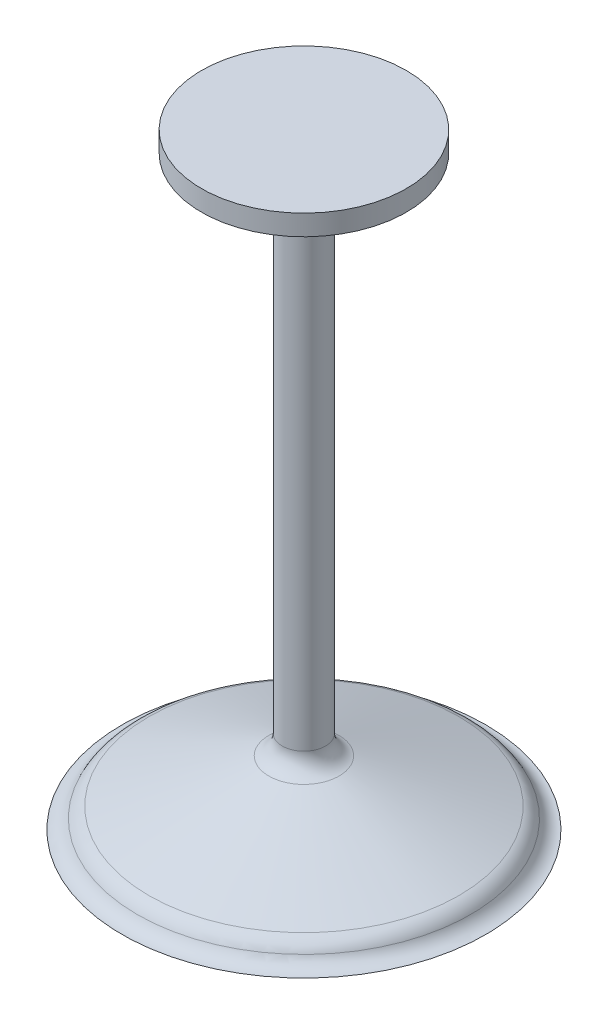
SolidWorks part; units mm, degrees
material "Plain Carbon Steel"
ref_plane "Front Plane" through (0, 0, 0) normal (0, 0, 1) x (1, 0, 0)
ref_plane "Top Plane" through (0, 0, 0) normal (0, 1, 0) x (1, 0, 0)
ref_plane "Right Plane" through (0, 0, 0) normal (1, 0, 0) x (0, 0, -1)
sketch "Sketch1" plane through (0, 0, 0) normal (0, 0, 1) x (1, 0, 0)
  line L0 (-44.8846, 0) -> (44.8846, 0) construction
  line L1 (0, -88.8) -> (0, 88.8) construction
  line L2 (23.5181, 0) -> (26.625, 0)
  line L3 (26.625, 0) -> (26.625, 2.45) construction
  line L4 (26.625, 2.45) -> (24.175, 2.45) construction
  line L5 (22.7023, 2.986) -> (5.1489, 9.3749)
  line L6 (3.175, 12.194) -> (3.175, 85.8)
  line L7 (3.175, 85.8) -> (15, 85.8)
  line L8 (15, 85.8) -> (15, 88.8)
  line L9 (15, 88.8) -> (0, 88.8)
  line L10 (0, 88.8) -> (0, 5)
  line L11 (0, 5) -> (19, 0) construction
  arc A0 (0, 5) -> (15.6481, 1.6135) centre (-0.9184, -37.09) cw
  arc A1 (24.4003, 1.4237) -> (26.625, 0) centre (26.625, 2.45) ccw
  arc A2 (24.4003, 1.4237) -> (22.7023, 2.986) centre (21.6763, 0.1669) ccw
  arc A3 (3.175, 12.194) -> (5.1489, 9.3749) centre (6.175, 12.194) ccw
  arc A4 (23.5181, 0) -> (15.6481, 1.6135) centre (23.5181, 20) cw
  point P4 (0, 0)
  point P8 (0, 0)
  dimension "D11" = 42.1
  dimension "D12" = 3
  dimension "D13" = 20
  dimension "D1" = 3
  dimension "D2" = 88.8
  dimension "D3" = 19
  dimension "D4" = 7.625
  dimension "D5" = 5
  dimension "D6" = 2.45
  dimension "D7" = 110
  dimension "D8" = 3.175
  dimension "D9" = 15
  dimension "D10" = 2.45
revolve "Revolve1" add sketch "Sketch1" angle 360 about L1
